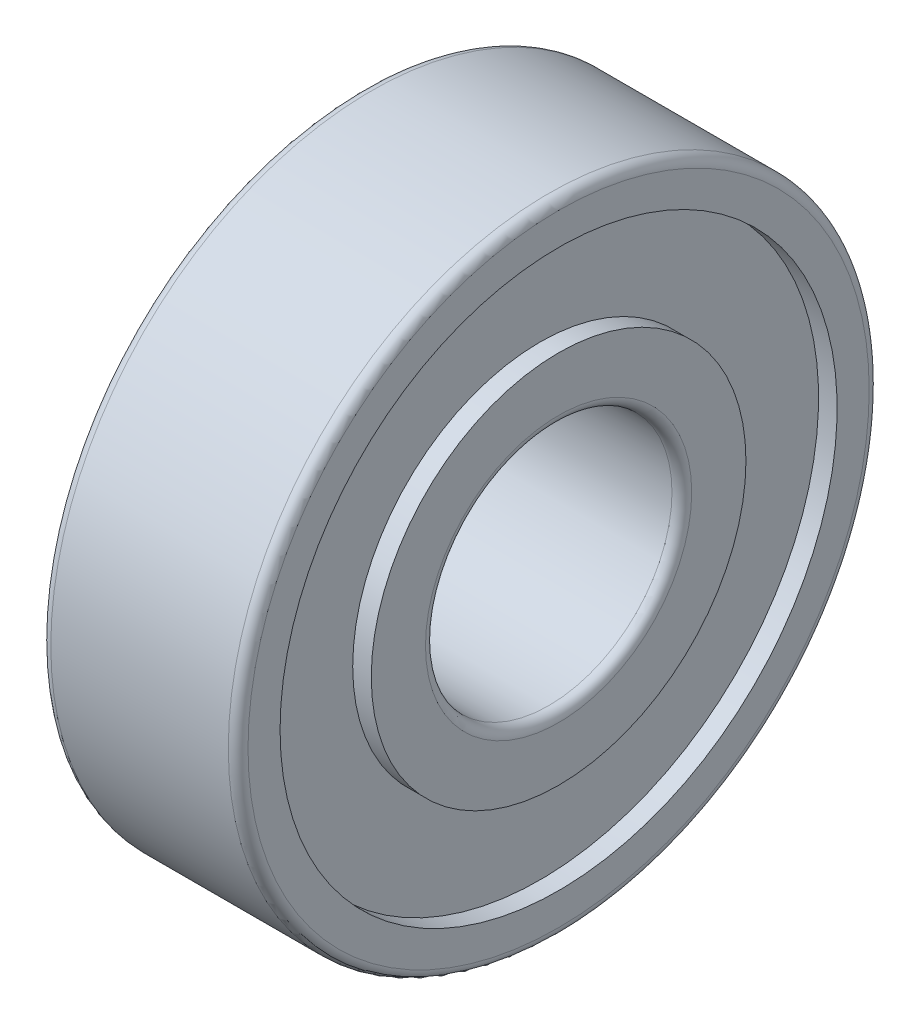
SolidWorks part; units mm, degrees
ref_plane "Front Plane" through (0, 0, 0) normal (0, 0, 1) x (1, 0, 0)
ref_plane "Top Plane" through (0, 0, 0) normal (0, 1, 0) x (1, 0, 0)
ref_plane "Right Plane" through (0, 0, 0) normal (1, 0, 0) x (0, 0, -1)
ref_plane "Plane1" through (0, 0, 0) normal (0, 0, 1) x (1, 0, 0)
sketch "Sketch1" plane through (0, 0, 0) normal (0, 0, 1) x (1, 0, 0)
  line L0 (0, 6.3) -> (0, 5.65)
  line L1 (0, 5.65) -> (0.3765, 5.65)
  line L2 (0.3765, 5.65) -> (0.3765, 3.8)
  line L3 (0.3765, 3.8) -> (0, 3.8)
  line L4 (0, 3.8) -> (0, 2.7)
  line L5 (0.2, 2.5) -> (3.8, 2.5)
  line L6 (4, 2.7) -> (4, 3.8)
  line L7 (4, 3.8) -> (3.6235, 3.8)
  line L8 (3.6235, 3.8) -> (3.6235, 5.65)
  line L9 (3.6235, 5.65) -> (4, 5.65)
  line L10 (4, 5.65) -> (4, 6.3)
  line L11 (3.8, 6.5) -> (0.2, 6.5)
  line L12 (3.8, 0) -> (0.2, 0) construction
  arc A0 (0, 2.7) -> (0.2, 2.5) centre (0.2, 2.7) ccw
  arc A1 (3.8, 2.5) -> (4, 2.7) centre (3.8, 2.7) ccw
  arc A2 (4, 6.3) -> (3.8, 6.5) centre (3.8, 6.3) ccw
  arc A3 (0.2, 6.5) -> (0, 6.3) centre (0.2, 6.3) ccw
revolve "Revolve1" add sketch "Sketch1" angle 360 about L12
